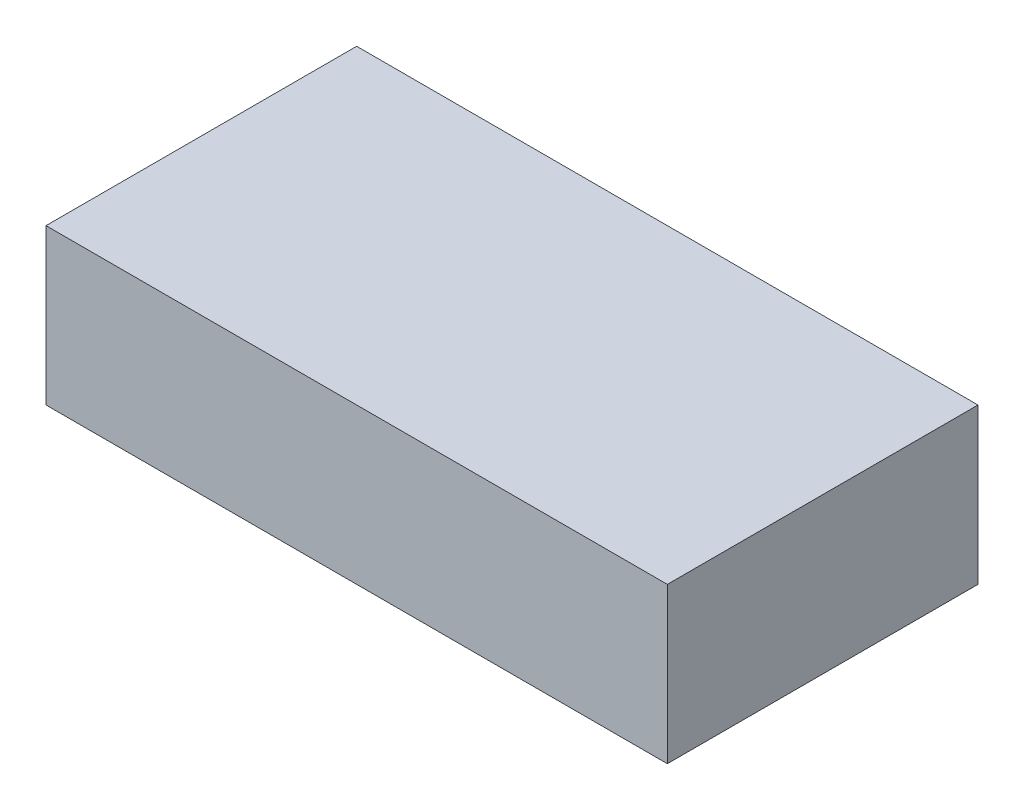
SolidWorks part; units mm, degrees
ref_plane "Front Plane" through (0, 0, 0) normal (0, 0, 1) x (1, 0, 0)
ref_plane "Top Plane" through (0, 0, 0) normal (0, 1, 0) x (1, 0, 0)
ref_plane "Right Plane" through (0, 0, 0) normal (1, 0, 0) x (0, 0, -1)
sketch "Sketch1" plane through (0, 0, 0) normal (0, 1, 0) x (1, 0, 0)
  line L1 (0, 0) -> (50.8, 0)
  line L2 (0, 0) -> (0, 25.4)
  line L3 (0, 25.4) -> (50.8, 25.4)
  line L4 (50.8, 0) -> (50.8, 25.4)
  dimension "D1" = 50.8
  dimension "D2" = 25.4
extrude "Boss-Extrude1" add sketch "Sketch1" along normal mid plane 12.7
